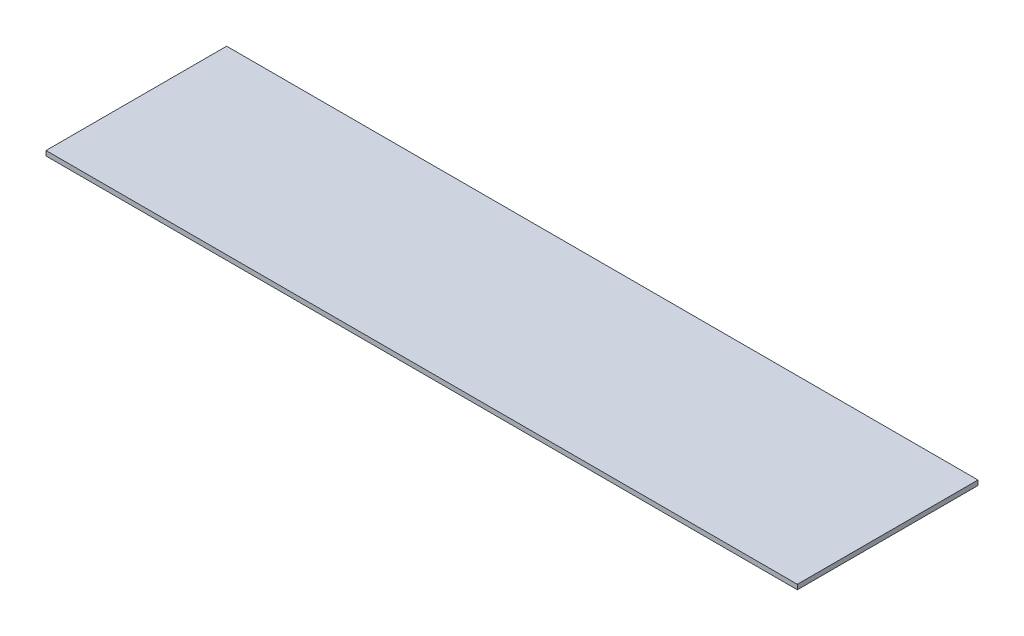
SolidWorks part; units mm, degrees
material "Pino"
ref_plane "Alzado" through (0, 0, 0) normal (0, 0, 1) x (1, 0, 0)
ref_plane "Planta" through (0, 0, 0) normal (0, 1, 0) x (1, 0, 0)
ref_plane "Vista lateral" through (0, 0, 0) normal (1, 0, 0) x (0, 0, -1)
sketch "Sketch1" plane through (0, 0, 0) normal (0, 1, 0) x (1, 0, 0)
  line L1 (-235, -56.5) -> (235, -56.5)
  line L2 (-235, -56.5) -> (-235, 56.5)
  line L3 (-235, 56.5) -> (235, 56.5)
  line L4 (235, -56.5) -> (235, 56.5)
  line L5 (-235, -56.5) -> (235, 56.5) construction
  line L6 (-235, 56.5) -> (235, -56.5) construction
  point P0 (0, 0)
  dimension "D1" = 470
  dimension "D2" = 113
extrude "Extrude1" add sketch "Sketch1" along normal blind 3
